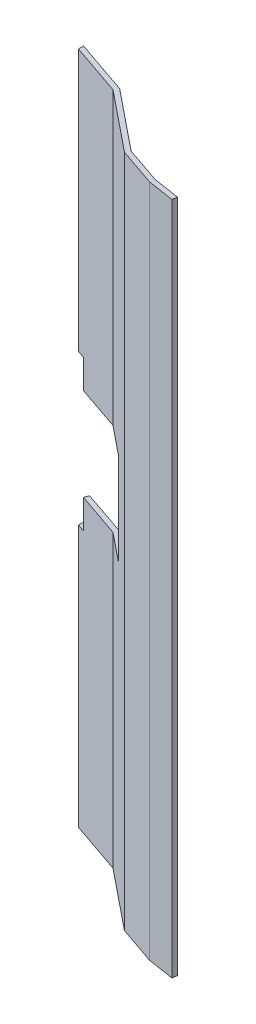
SolidWorks part; units mm, degrees
ref_plane "Front Plane" through (0, 0, 0) normal (0, 0, 1) x (1, 0, 0)
ref_plane "Top Plane" through (0, 0, 0) normal (0, 1, 0) x (1, 0, 0)
ref_plane "Right Plane" through (0, 0, 0) normal (1, 0, 0) x (0, 0, -1)
sketch "Sketch1" plane through (0, 0, 0) normal (0, 1, 0) x (1, 0, 0)
  line B0 (-37.0626, 23.5832) -> (-37.0626, 21.9048)
  line B1 (-18.9754, 17.3756) -> (-37.0626, 23.5832)
  line B2 (21.3237, -5.6863) -> (21.5743, -4.0939)
  line B3 (12.7923, -2.712) -> (21.5743, -4.0939)
  line B4 (-18.9754, 17.3756) -> (0.7801, 1.4107)
  line B5 (0.7801, 1.4107) -> (12.7923, -2.712)
  line B6 (21.3237, -5.6863) -> (12.5417, -4.3044)
  line B7 (12.5417, -4.3044) -> (0, 0)
  line B8 (0, 0) -> (-19.7555, 15.9649)
  line B9 (-19.7555, 15.9649) -> (-37.0626, 21.9048)
  line B10 (-37.0626, 21.9048) -> (-37.0626, 23.5832)
sketch_block_instance "Wedge sketch block-1"
sketch_block "Wedge sketch block" parameters "D1"=160, "D2"=25.4, "D3"=170, "D4"=1.5875, "D5"=1.5875, "D6"=1.5875, "D7"=160, "D8"=8.89, "D9"=8.89, "D10"=12.7
sketch "Sketch3" plane through (0, 0, 0) normal (0, 1, 0) x (1, 0, 0)
  line L0 (-37.0626, 21.9048) -> (-19.7555, 15.9649)
  line L1 (-19.7555, 15.9649) -> (0, 0)
  line L2 (0, 0) -> (12.5417, -4.3044)
  line L3 (12.5417, -4.3044) -> (21.3237, -5.6863)
  line L4 (21.3237, -5.6863) -> (21.5743, -4.0939)
  line L5 (21.5743, -4.0939) -> (12.7923, -2.712)
  line L6 (12.7923, -2.712) -> (0.7801, 1.4107)
  line L7 (0.7801, 1.4107) -> (-18.9754, 17.3756)
  line L8 (-18.9754, 17.3756) -> (-37.0626, 23.5832)
  line L9 (-37.0626, 23.5832) -> (-37.0626, 21.9048)
  point P4 (0, 0)
  dimension "D1" = 160
  dimension "D2" = 25.4
  dimension "D3" = 1.5875
  dimension "D4" = 1.5875
  dimension "D5" = 19.1227
extrude "Boss-Extrude2" add sketch "Sketch3" along normal blind 222.25
sketch "Sketch4" plane through (3.3354, 0, -9.7184) normal (0.3246, 0, -0.9458) x (-0.9458, 0, -0.3246)
  line L0 (42.711, 222.25) -> (42.711, 0) construction
  line L1 (42.711, 126.365) -> (12.231, 126.365)
  line L2 (42.711, 126.365) -> (42.711, 95.885)
  line L3 (42.711, 95.885) -> (12.231, 95.885)
  line L4 (12.231, 126.365) -> (12.231, 95.885)
  line L6 (-0.2799, 222.25) -> (23.5883, 222.25) construction
  line L7 (23.5883, 0) -> (42.711, 0) construction
  line L9 (42.711, 126.365) -> (39.536, 126.365)
  line L10 (42.711, 126.365) -> (42.711, 135.89)
  line L11 (42.711, 135.89) -> (39.536, 135.89)
  line L12 (39.536, 126.365) -> (39.536, 135.89)
  line L13 (42.711, 95.885) -> (39.536, 95.885)
  line L14 (42.711, 95.885) -> (42.711, 86.36)
  line L15 (42.711, 86.36) -> (39.536, 86.36)
  line L16 (39.536, 95.885) -> (39.536, 86.36)
  line M6 (42.711, 0) -> (42.711, 222.25)
  line M8 (23.5883, 222.25) -> (23.5883, 0)
  dimension "D1" = 95.885
  dimension "D2" = 95.885
  dimension "D3" = 30.48
  dimension "D4" = 3.175
  dimension "D5" = 3.175
  dimension "D6" = 9.525
  dimension "D7" = 9.525
extrude "Cut-Extrude2" cut sketch "Sketch4" against normal through all both and the other way through all contours L12 L1 L11 M6 | L3 L1 M6 M8 | L3 L16 L15 M6 | L1 L4 L3 M8
